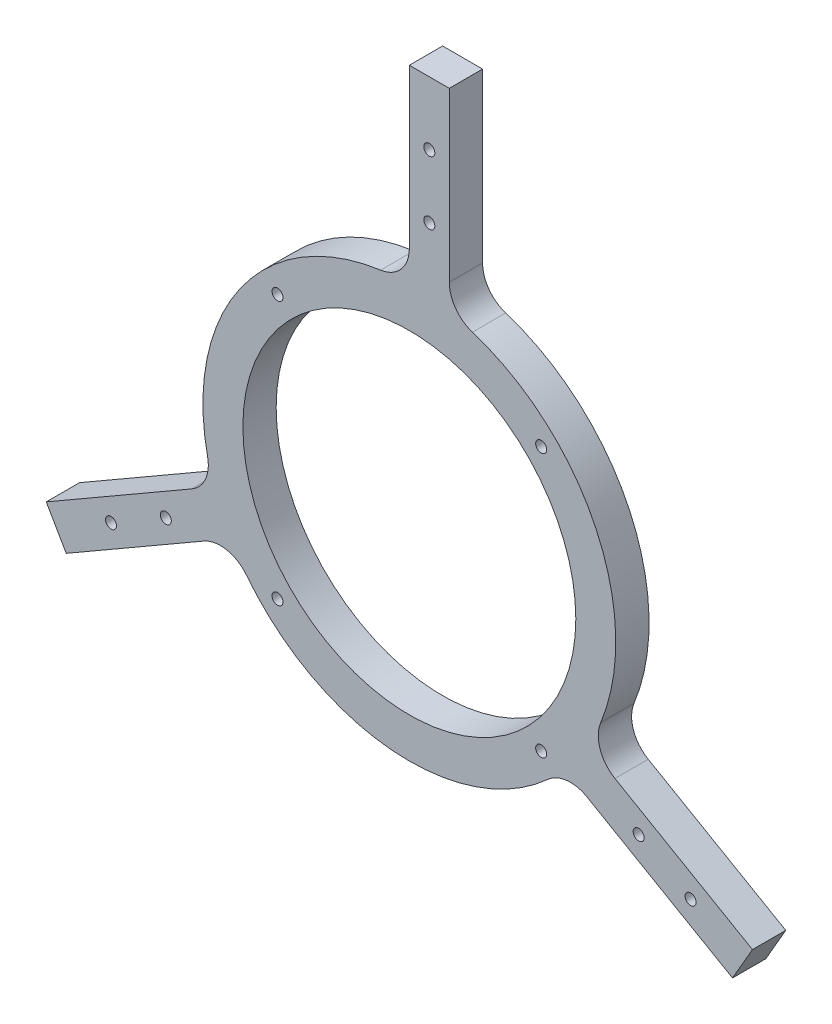
SolidWorks part; units mm, degrees
ref_plane "前视基准面" through (0, 0, 0) normal (0, 0, 1) x (1, 0, 0)
ref_plane "上视基准面" through (0, 0, 0) normal (0, 1, 0) x (1, 0, 0)
ref_plane "右视基准面" through (0, 0, 0) normal (1, 0, 0) x (0, 0, -1)
sketch "草图1" plane through (0, 0, 0) normal (0, 0, 1) x (1, 0, 0)
  line L0 (0, 0) -> (0, 62)
  line L1 (0, 62) -> (53.6936, -31)
  line L2 (0, 62) -> (-53.6936, -31)
  line L3 (-53.6936, -31) -> (53.6936, -31)
  line L4 (0, 0) -> (-53.6936, -31)
  line L5 (0, 0) -> (53.6936, -31)
  line L6 (-53.6936, -31) -> (-12.251, -7.0731)
  line L7 (0, 62) -> (12, 62)
  line L8 (0, 62) -> (0, 7.4328)
  line L9 (0, 7.4328) -> (12, 7.4328)
  line L10 (12, 62) -> (12, 7.4328)
  line L11 (-53.6936, -31) -> (-59.6936, -20.6077)
  line L12 (-12.251, -7.0731) -> (-18.251, 3.3192)
  line L13 (-59.6936, -20.6077) -> (-18.251, 3.3192)
  line L14 (53.6936, -31) -> (6.3112, -3.6438)
  line L15 (53.6936, -31) -> (47.6936, -41.3923)
  line L16 (6.3112, -3.6438) -> (0.3112, -14.0361)
  line L17 (47.6936, -41.3923) -> (0.3112, -14.0361)
  line L18 (-53.6936, -31) -> (-59.6936, -20.6077)
  line L19 (-53.6936, -31) -> (-103.057, -59.5)
  line L20 (-59.6936, -20.6077) -> (-109.057, -49.1077)
  line L21 (-103.057, -59.5) -> (-109.057, -49.1077)
  line L22 (0, 62) -> (12, 62)
  line L23 (0, 62) -> (0, 119)
  line L24 (12, 62) -> (12, 119)
  line L25 (0, 119) -> (12, 119)
  line L26 (47.6936, -41.3923) -> (53.6936, -31)
  line L27 (47.6936, -41.3923) -> (97.057, -69.8923)
  line L28 (53.6936, -31) -> (103.057, -59.5)
  line L29 (97.057, -69.8923) -> (103.057, -59.5)
  circle A0 centre (0, 0) radius 62
  circle A1 centre (0, 0) radius 50
  circle A2 centre (0, 0) radius 100
extrude "凸台-拉伸1" add sketch "草图1" along normal blind 10 contours L17 A0 L3 | A0 L17 L15 | L13 A0 L2 | A0 L13 L11 | L10 A0 L1 | A0 L10 L7 | L13 A2 L6 A1 | L17 A2 L14 A1 | L10 A2 L8 A1 | L25 L23 L7 L24 | L21 L19 L11 L20 | L27 L29 L28 L15 | L20 A2 L19 L11 | L27 A2 L28 L15 | L24 A2 L23 L7 | A1 L1 A0 L10 | A1 L2 A0 L13 | A1 L3 A0 L17 | A1 L6 L3 | A1 L14 L1 | A1 L8 L2
sketch "草图4" plane through (0, 0, 10) normal (0, 0, 1) x (1, 0, 0)
  line L0 (-106.057, -54.3038) -> (-73.1481, -35.3038)
  line L1 (-103.057, -59.5) -> (-109.057, -49.1077) construction
  line L2 (6, 119) -> (6, 81)
  line L3 (0, 119) -> (12, 119) construction
  line L4 (100.057, -64.6962) -> (68.8801, -46.6962)
  line L5 (97.057, -69.8923) -> (103.057, -59.5) construction
  line L6 (0, 0) -> (43.8406, 43.8406)
  line L7 (0, 0) -> (0, 56.3958)
  line L8 (0, 0) -> (-40.2969, 40.2969)
  line L9 (0, 0) -> (-40.2969, -40.2969)
  line L10 (0, 0) -> (41.4725, -41.4725)
  arc A0 (53.6936, -31) -> (12, 60.8276) centre (0, 0) ccw construction
  circle A1 centre (0, 0) radius 56
hole_wizard "M4 螺纹孔1" positions "草图5" profile "草图6" tap size "M4" standard "GB"
sketch "草图5" plane through (0, 0, 10) normal (0, 0, 1) x (1, 0, 0)
  line L0 (0, 0) -> (-40.2969, 40.2969) construction
  line L1 (0, 0) -> (-40.2969, -40.2969) construction
  line L2 (0, 0) -> (41.4725, -41.4725) construction
  line L3 (0, 0) -> (43.8406, 43.8406) construction
  line L4 (-106.057, -54.3038) -> (-73.1481, -35.3038) construction
  line L5 (100.057, -64.6962) -> (68.8801, -46.6962) construction
  line L6 (6, 119) -> (6, 81) construction
  circle A0 centre (0, 0) radius 56 construction
  point P0 (-39.598, 39.598)
  point P6 (-39.598, -39.598)
  point P10 (39.598, -39.598)
  point P14 (39.598, 39.598)
  point P21 (-89.6025, -44.8038)
  point P25 (-73.1481, -35.3038)
  point P28 (84.4686, -55.6962)
  point P32 (68.8801, -46.6962)
  point P35 (6, 81)
  point P38 (6, 100)
sketch "草图6" plane through (-39.598, 39.598, 10) normal (1, 0, 0) x (0, -1, 0)
  line L0 (0, 0) -> (0, 11.0914)
  line L1 (0, 11.0914) -> (1.65, 10.1)
  line L2 (1.65, 10.1) -> (1.65, 0)
  line L5 (1.65, 0) -> (0, 0)
  line L10 (0, 11.0914) -> (-1.65, 10.1) construction
  line L11 (0, -6.35) -> (0, 107.95) construction
  dimension "螺纹孔钻头直径" = 3.3
  dimension "螺纹孔钻头深度" = 10.1
  dimension "导头角度" = 118
cosmetic thread "孔螺蚊线1" parameters "D1"=8, "D2"=4
cosmetic thread "孔螺蚊线2" parameters "D1"=8, "D2"=4
cosmetic thread "孔螺蚊线3" parameters "D1"=8, "D2"=4
cosmetic thread "孔螺蚊线4" parameters "D1"=8, "D2"=4
cosmetic thread "孔螺蚊线5" parameters "D1"=8, "D2"=4
cosmetic thread "孔螺蚊线6" parameters "D1"=8, "D2"=4
cosmetic thread "孔螺蚊线7" parameters "D1"=8, "D2"=4
cosmetic thread "孔螺蚊线8" parameters "D1"=8, "D2"=4
cosmetic thread "孔螺蚊线9" parameters "D1"=8, "D2"=4
cosmetic thread "孔螺蚊线10" parameters "D1"=8, "D2"=4
fillet "圆角1" radius 10 6 edges at (0, 62, 5) (12, 60.8276, 5) (53.6936, -31, 5) (46.6783, -40.8061, 5) (-53.6936, -31, 5) (-58.6783, -20.0215, 5)
